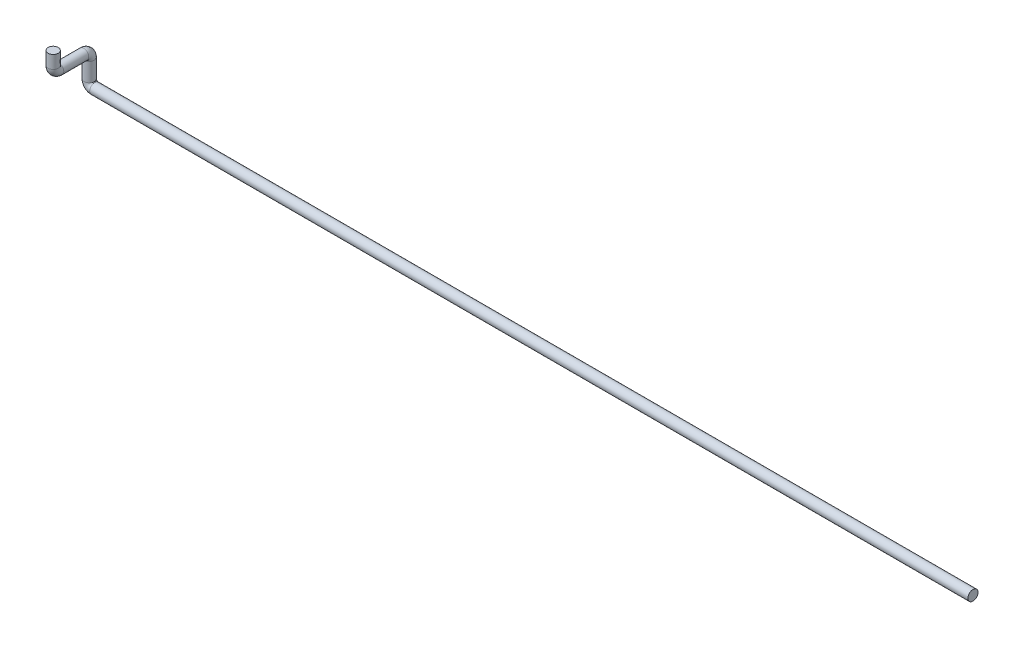
SolidWorks part; units mm, degrees
ref_plane "Alzado" through (0, 0, 0) normal (0, 0, 1) x (1, 0, 0)
ref_plane "Planta" through (0, 0, 0) normal (0, 1, 0) x (1, 0, 0)
ref_plane "Vista lateral" through (0, 0, 0) normal (1, 0, 0) x (0, 0, -1)
sketch3d "Croquis3D1"
  line L0 (0, 0, 0) -> (-2374, 0, 0)
  line L1 (-2389, 15, 0) -> (-2389, 65, 0)
  line L2 (-2389, 80, 15) -> (-2389, 80, 82.5)
  line L3 (-2389, 95, 97.5) -> (-2389, 130, 97.5)
  arc A0 (-2389, 65, 0) -> (-2389, 80, 15) centre (-2389, 65, 15) ccw
  arc A1 (-2374, 0, 0) -> (-2389, 15, 0) centre (-2374, 15, 0) ccw
  arc A2 (-2389, 80, 82.5) -> (-2389, 95, 97.5) centre (-2389, 95, 82.5) ccw
  point P8 (-2389, 80, 0)
  point P9 (-2374, 65, 15)
  point P12 (-2389, 0, 0)
  point P13 (-2374, 15, -15)
  point P16 (-2389, 80, 97.5)
  point P17 (-2404, 95, 82.5)
  dimension "D5" = 15
  dimension "D1" = 2389
  dimension "D2" = 80
  dimension "D3" = 97.5
  dimension "D4" = 50
sketch "Croquis1" plane through (0, 0, 0) normal (1, 0, 0) x (0, 0, -1)
  circle A0 centre (0, 0) radius 13.7
  dimension "D1" = 27.4
sweep "Barrer1" add profiles "Croquis1" path "Croquis3D1"
